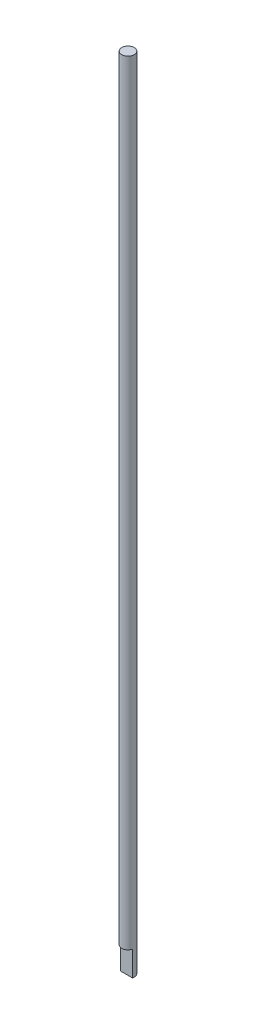
SolidWorks part; units mm, degrees
ref_plane "Front Plane" through (0, 0, 0) normal (0, 0, 1) x (1, 0, 0)
ref_plane "Top Plane" through (0, 0, 0) normal (0, 1, 0) x (1, 0, 0)
ref_plane "Right Plane" through (0, 0, 0) normal (1, 0, 0) x (0, 0, -1)
sketch "Sketch1" plane through (0, 0, 0) normal (0, 1, 0) x (1, 0, 0)
  circle A0 centre (0, 0) radius 3.175
  dimension "D1" = 6.35
extrude "Boss-Extrude1" add sketch "Sketch1" along normal blind 406.4
sketch "Sketch2" plane through (0, 0, 0) normal (0, -1, 0) x (1, 0, 0)
  line L1 (-3.7817, 0.777) -> (3.8087, 0.777)
  line L2 (-3.7817, 0.777) -> (-3.7817, 3.373)
  line L3 (-3.7817, 3.373) -> (3.8087, 3.373)
  line L4 (3.8087, 0.777) -> (3.8087, 3.373)
extrude "Cut-Extrude1" cut sketch "Sketch2" against normal blind 12.7
